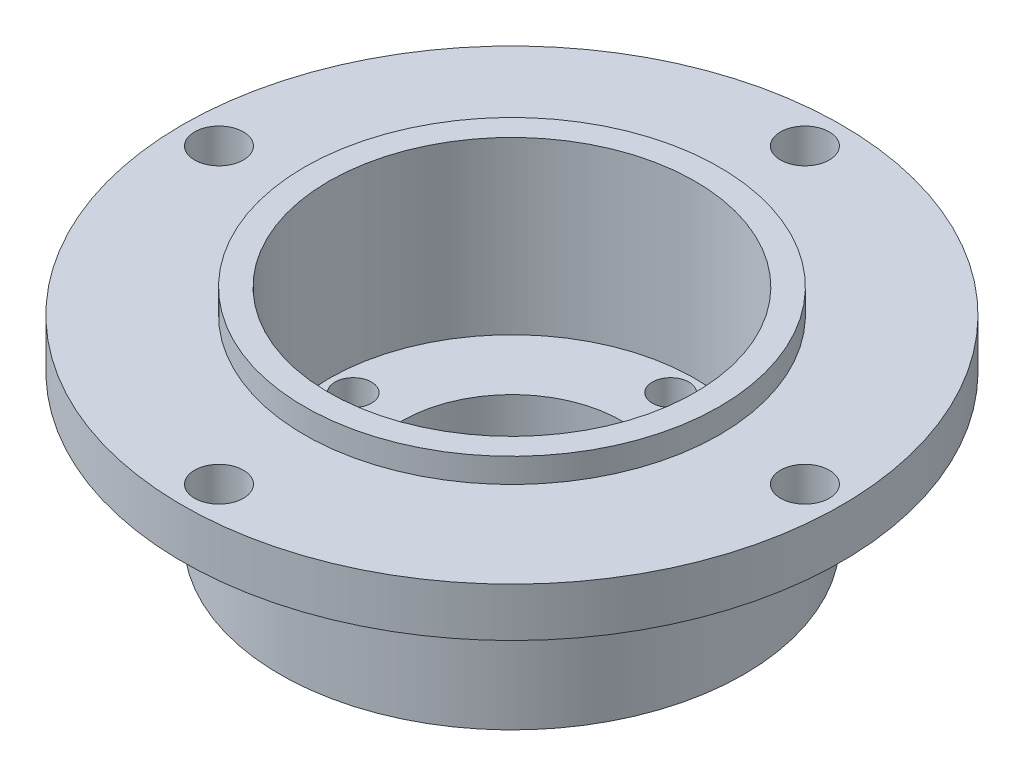
SolidWorks part; units mm, degrees
ref_plane "Plan de face" through (0, 0, 0) normal (0, 0, 1) x (1, 0, 0)
ref_plane "Plan de dessus" through (0, 0, 0) normal (0, 1, 0) x (1, 0, 0)
ref_plane "Plan de droite" through (0, 0, 0) normal (1, 0, 0) x (0, 0, -1)
sketch "Esquisse1" plane through (0, 0, 0) normal (0, 0, 1) x (1, 0, 0)
  line L0 (0, 0) -> (0, -20) construction
  line L1 (19, -12) -> (27, -12)
  line L2 (15, -20) -> (15, -6)
  line L3 (15, -20) -> (9, -20)
  line L5 (27, -8) -> (27, -12)
  line L6 (9, -24) -> (19, -24)
  line L7 (9, -20) -> (9, -24)
  line L9 (19, -24) -> (19, -12)
  line L10 (27, -8) -> (17, -8)
  line L14 (17, -6) -> (15, -6)
  line L15 (17, -8) -> (17, -6)
  line L16 (17, -20) -> (17, -6) construction
revolve "Révolution1" add sketch "Esquisse1" angle 360 about L0
sketch "Esquisse3" plane through (0, -12, 0) normal (0, -1, 0) x (1, 0, 0)
  circle A3 centre (24, 0) radius 2
  circle A4 centre (0, 24) radius 2
  circle A5 centre (0, -24) radius 2
  circle A6 centre (-24, 0) radius 2
sketch "Esquisse4" plane through (0, -24, 0) normal (0, -1, 0) x (1, 0, 0)
  line L0 (0, 0) -> (0, 13) construction
  circle A0 centre (0, 13) radius 1.5
  circle A1 centre (13, 0) radius 1.5
  circle A2 centre (0, -13) radius 1.5
  circle A3 centre (-13, 0) radius 1.5
extrude "Extrusion3" cut sketch "Esquisse4" against normal through all
extrude "Extrusion4" cut sketch "Esquisse3" against normal through all
